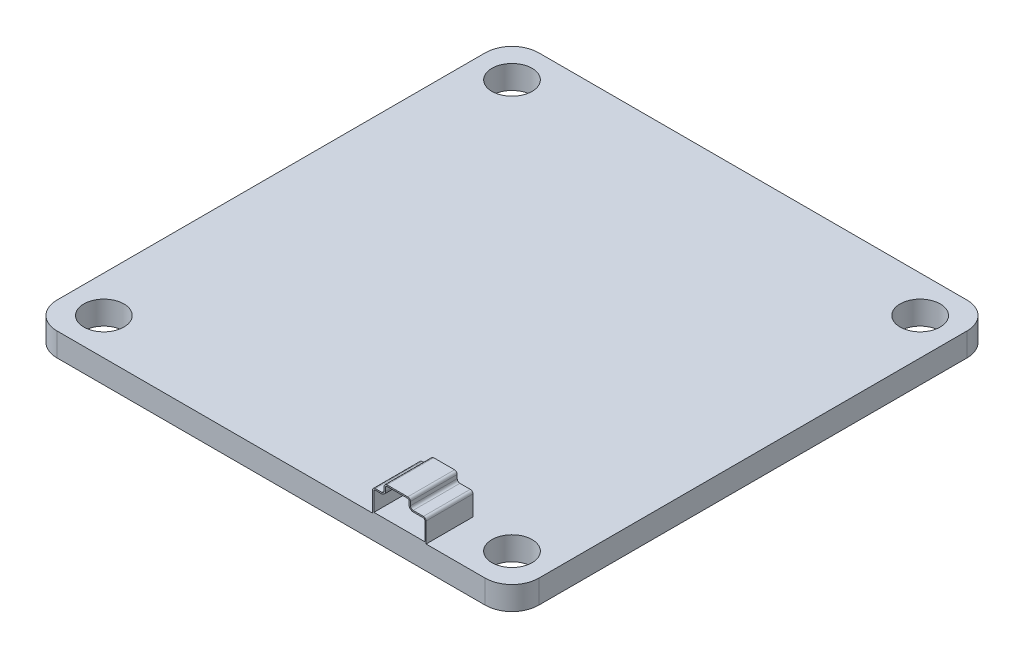
SolidWorks part; units mm, degrees
ref_plane "Front Plane" through (0, 0, 0) normal (0, 0, 1) x (1, 0, 0)
ref_plane "Top Plane" through (0, 0, 0) normal (0, 1, 0) x (1, 0, 0)
ref_plane "Right Plane" through (0, 0, 0) normal (1, 0, 0) x (0, 0, -1)
sketch "Sketch1" plane through (0, 0, 0) normal (0, 1, 0) x (1, 0, 0)
  line L1 (-16, 18) -> (16, 18)
  line L2 (-18, 16) -> (-18, -16)
  line L3 (-16, -18) -> (16, -18)
  line L4 (18, 16) -> (18, -16)
  line L5 (-18, 18) -> (18, -18) construction
  line L6 (-18, -18) -> (18, 18) construction
  line L7 (-15.25, 15.25) -> (15.25, 15.25) construction
  line L8 (-15.25, 15.25) -> (-15.25, -15.25) construction
  line L9 (-15.25, -15.25) -> (15.25, -15.25) construction
  line L10 (15.25, 15.25) -> (15.25, -15.25) construction
  line L11 (-15.25, 15.25) -> (15.25, -15.25) construction
  line L12 (-15.25, -15.25) -> (15.25, 15.25) construction
  circle A0 centre (-15.25, 15.25) radius 1.5
  circle A1 centre (15.25, 15.25) radius 1.5
  circle A2 centre (15.25, -15.25) radius 1.5
  circle A3 centre (-15.25, -15.25) radius 1.5
  arc A4 (-16, -18) -> (-18, -16) centre (-16, -16) cw
  arc A5 (16, -18) -> (18, -16) centre (16, -16) ccw
  arc A6 (18, 16) -> (16, 18) centre (16, 16) ccw
  arc A7 (-16, 18) -> (-18, 16) centre (-16, 16) ccw
  point P0 (0, 0)
  point P6 (0, 0)
  point P27 (-77.7756, 4.9038)
  dimension "D3" = 3
  dimension "D4" = 2
  dimension "D5" = 2
  dimension "D6" = 2
  dimension "D7" = 2
  dimension "D1" = 36
  dimension "D2" = 30.5
extrude "Boss-Extrude1" add sketch "Sketch1" along normal blind 1.75
sketch "Sketch2" plane through (0, 0, 18) normal (0, 0, 1) x (1, 0, 0)
  line L0 (-16, 1.75) -> (16, 1.75) construction
  line L1 (7.5808, 1.75) -> (11.5808, 1.75)
  line L2 (7.5808, 1.75) -> (7.5808, 3.24)
  line L3 (8.6481, 4.1176) -> (10.2074, 4.1176)
  line L4 (11.5808, 1.75) -> (11.5808, 3.24)
  line L5 (7.7808, 3.44) -> (8.2481, 3.44)
  line L6 (8.4481, 3.64) -> (8.4481, 3.9176)
  line L7 (11.3808, 3.44) -> (10.6074, 3.44)
  line L8 (10.4074, 3.64) -> (10.4074, 3.9176)
  line L9 (8.6481, 4.0176) -> (10.2074, 4.0176)
  line L10 (10.3074, 3.64) -> (10.3074, 3.9176)
  line L11 (11.3808, 3.34) -> (10.6074, 3.34)
  line L12 (11.4808, 1.85) -> (11.4808, 3.24)
  line L13 (7.6808, 1.85) -> (11.4808, 1.85)
  line L14 (7.6808, 1.85) -> (7.6808, 3.24)
  line L15 (7.7808, 3.34) -> (8.2481, 3.34)
  line L16 (8.5481, 3.64) -> (8.5481, 3.9176)
  arc A0 (11.5808, 3.24) -> (11.3808, 3.44) centre (11.3808, 3.24) ccw
  arc A1 (7.7808, 3.44) -> (7.5808, 3.24) centre (7.7808, 3.24) ccw
  arc A2 (8.4481, 3.64) -> (8.2481, 3.44) centre (8.2481, 3.64) cw
  arc A3 (10.6074, 3.44) -> (10.4074, 3.64) centre (10.6074, 3.64) cw
  arc A4 (10.4074, 3.9176) -> (10.2074, 4.1176) centre (10.2074, 3.9176) ccw
  arc A5 (8.4481, 3.9176) -> (8.6481, 4.1176) centre (8.6481, 3.9176) cw
  arc A6 (10.3074, 3.9176) -> (10.2074, 4.0176) centre (10.2074, 3.9176) ccw
  arc A7 (10.6074, 3.34) -> (10.3074, 3.64) centre (10.6074, 3.64) cw
  arc A8 (11.4808, 3.24) -> (11.3808, 3.34) centre (11.3808, 3.24) ccw
  arc A9 (7.7808, 3.34) -> (7.6808, 3.24) centre (7.7808, 3.24) ccw
  arc A10 (8.5481, 3.64) -> (8.2481, 3.34) centre (8.2481, 3.64) cw
  arc A11 (8.5481, 3.9176) -> (8.6481, 4.0176) centre (8.6481, 3.9176) cw
  point P16 (8.4481, 3.44)
  point P23 (3.963, 4.9256)
  dimension "D1" = 0.2
  dimension "D2" = 0.2
  dimension "D3" = 0.2
  dimension "D4" = 0.2
  dimension "D5" = 0.2
  dimension "D6" = 0.2
  dimension "D7" = 0.1
extrude "Boss-Extrude4" add sketch "Sketch2" against normal blind 3
sketch "Sketch5" plane through (0, 0, 15) normal (0, 0, -1) x (-1, 0, 0)
  line L8 (-7.5808, 1.75) -> (-7.5808, 3.24)
  line L9 (-7.7808, 3.44) -> (-8.2481, 3.44)
  line L10 (-8.4481, 3.64) -> (-8.4481, 3.9176)
  line L11 (-8.6481, 4.1176) -> (-10.2074, 4.1176)
  line L12 (-10.4074, 3.9176) -> (-10.4074, 3.64)
  line L13 (-10.6074, 3.44) -> (-11.3808, 3.44)
  line L14 (-11.5808, 3.24) -> (-11.5808, 1.75)
  line L15 (-11.5808, 1.75) -> (-7.5808, 1.75)
  line L16 (-7.5808, 1.75) -> (-7.5808, 3.24)
  line L17 (-7.7808, 3.44) -> (-8.2481, 3.44)
  line L18 (-8.4481, 3.64) -> (-8.4481, 3.9176)
  line L19 (-8.6481, 4.1176) -> (-10.2074, 4.1176)
  line L20 (-10.4074, 3.9176) -> (-10.4074, 3.64)
  line L21 (-10.6074, 3.44) -> (-11.3808, 3.44)
  line L22 (-11.5808, 3.24) -> (-11.5808, 1.75)
  line L23 (-11.5808, 1.75) -> (-7.5808, 1.75)
  arc A6 (-7.5808, 3.24) -> (-7.7808, 3.44) centre (-7.7808, 3.24) ccw
  arc A7 (-8.4481, 3.64) -> (-8.2481, 3.44) centre (-8.2481, 3.64) ccw
  arc A8 (-8.4481, 3.9176) -> (-8.6481, 4.1176) centre (-8.6481, 3.9176) ccw
  arc A9 (-10.2074, 4.1176) -> (-10.4074, 3.9176) centre (-10.2074, 3.9176) ccw
  arc A10 (-10.6074, 3.44) -> (-10.4074, 3.64) centre (-10.6074, 3.64) ccw
  arc A11 (-11.3808, 3.44) -> (-11.5808, 3.24) centre (-11.3808, 3.24) ccw
  arc A12 (-7.5808, 3.24) -> (-7.7808, 3.44) centre (-7.7808, 3.24) ccw
  arc A13 (-8.4481, 3.64) -> (-8.2481, 3.44) centre (-8.2481, 3.64) ccw
  arc A14 (-8.4481, 3.9176) -> (-8.6481, 4.1176) centre (-8.6481, 3.9176) ccw
  arc A15 (-10.2074, 4.1176) -> (-10.4074, 3.9176) centre (-10.2074, 3.9176) ccw
  arc A16 (-10.6074, 3.44) -> (-10.4074, 3.64) centre (-10.6074, 3.64) ccw
  arc A17 (-11.3808, 3.44) -> (-11.5808, 3.24) centre (-11.3808, 3.24) ccw
  dimension "D1" = 0
extrude "Boss-Extrude5" add sketch "Sketch5" along normal blind 0.5
sketch "Sketch7" plane through (0, 0, 14.5) normal (0, 0, -1) x (-1, 0, 0)
  circle A0 centre (-10.3024, 3.1993) radius 0.25
  circle A1 centre (-9.5024, 3.1993) radius 0.25
  circle A2 centre (-8.7024, 3.1993) radius 0.25
  dimension "D1" = 0.8
  dimension "D2" = 0.8
  dimension "D3" = 0.5
extrude "Cut-Extrude1" cut sketch "Sketch7" against normal up to next
